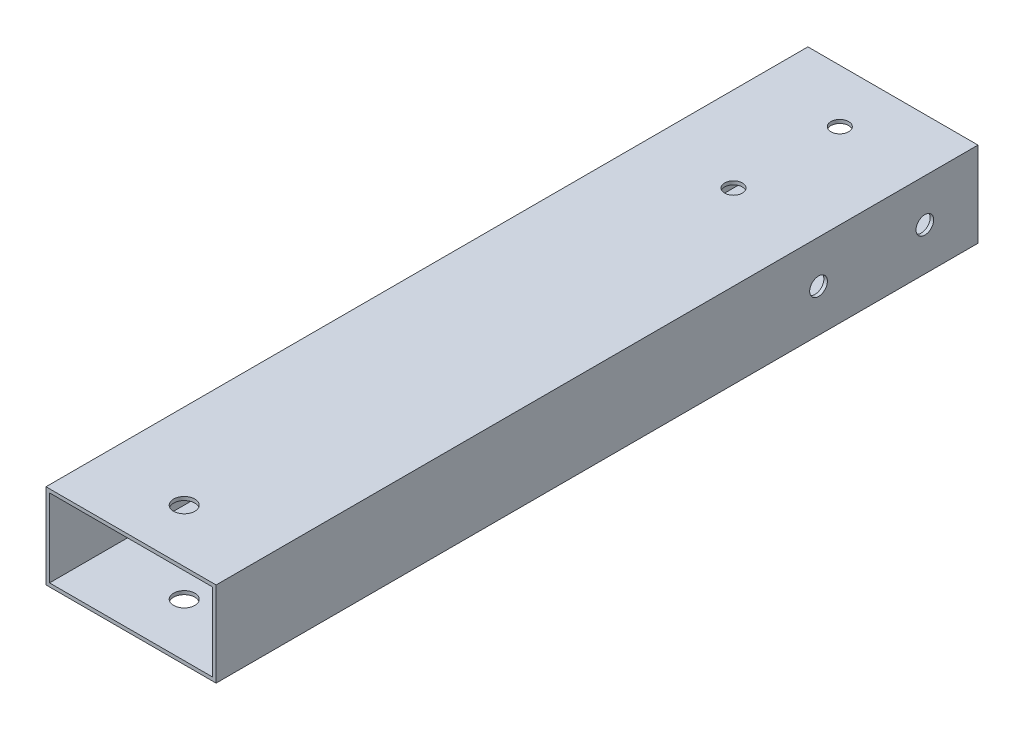
SolidWorks part; units mm, degrees
ref_plane "Front Plane" through (0, 0, 0) normal (0, 0, 1) x (1, 0, 0)
ref_plane "Top Plane" through (0, 0, 0) normal (0, 1, 0) x (1, 0, 0)
ref_plane "Right Plane" through (0, 0, 0) normal (1, 0, 0) x (0, 0, -1)
sketch "Sketch2" plane through (0, 0, 0) normal (0, 0, 1) x (1, 0, 0)
  line L0 (-23, 11) -> (-23, -11)
  line L1 (-24, 12) -> (24, 12)
  line L2 (-24, 12) -> (-24, -12)
  line L3 (-24, -12) -> (24, -12)
  line L4 (24, 12) -> (24, -12)
  line L5 (-24, 12) -> (24, -12) construction
  line L6 (-24, -12) -> (24, 12) construction
  line L7 (-23, -11) -> (23, -11)
  line L8 (23, 11) -> (23, -11)
  line L9 (-23, 11) -> (23, 11)
  point P0 (0, 0)
  dimension "D1" = 24
  dimension "D2" = 48
  dimension "D3" = 1
extrude "Boss-Extrude1" add sketch "Sketch2" along normal blind 240
sketch "Sketch4" plane through (0, -12, 0) normal (0, -1, 0) x (1, 0, 0)
  line L0 (-24, 240) -> (24, 240) construction
  line L1 (24, 240) -> (24, 0) construction
  circle A0 centre (0, 200) radius 3
  dimension "D2" = 6
  dimension "D3" = 24
  dimension "D1" = 40
extrude "Cut-Extrude1" cut sketch "Sketch4" against normal blind 240 contours A0
sketch "Sketch5" plane through (0, -12, 0) normal (0, -1, 0) x (1, 0, 0)
  line L0 (-9, 0) -> (9, 0)
  line L2 (-9, 0) -> (-9, 50)
  line L3 (-9, 50) -> (9, 50)
  line L4 (9, 0) -> (9, 50)
  line L5 (0, 50) -> (0, 0)
  circle A0 centre (0, 15) radius 2.5
  circle A1 centre (0, 45) radius 2.5
  point P0 (0, 0)
  point P8 (0, 0)
  dimension "D3" = 5
  dimension "D4" = 5
  dimension "D1" = 50
  dimension "D2" = 18
  dimension "D5" = 15
  dimension "D6" = 5
extrude "Cut-Extrude3" cut sketch "Sketch5" against normal blind 240 contours L5 A1 | L5 A1 | L5 A0 | L5 A0
sketch "Sketch7" plane through (24, 0, 0) normal (1, 0, 0) x (0, 0, -1)
  line L0 (0, -9) -> (0, 9)
  line L1 (0, -9) -> (-50, -9)
  line L2 (-50, -9) -> (-50, 9)
  line L3 (0, 9) -> (-50, 9)
  line L4 (-50, 0) -> (0, 0)
  circle A0 centre (-15, 0) radius 2.5
  circle A1 centre (-45, 0) radius 2.5
  point P0 (0, 0)
  point P7 (0, 0)
  dimension "D5" = 5
  dimension "D6" = 5
  dimension "D1" = 15
  dimension "D2" = 5
  dimension "D3" = 50
  dimension "D4" = 18
  dimension "D7" = 90
  dimension "D8" = 90
  dimension "D9" = 50
extrude "Cut-Extrude4" cut sketch "Sketch7" against normal blind 240 contours L4 A1 | L4 A1 | L4 A0 | L4 A0
sketch "Sketch8" plane through (0, -12, 0) normal (0, -1, 0) x (1, 0, 0)
  line L0 (24, 240) -> (24, 0) construction
  line L1 (-24, 240) -> (24, 240)
  line L2 (-24, 240) -> (-24, 215)
  line L3 (-24, 215) -> (24, 215)
  line L4 (24, 240) -> (24, 215)
  dimension "D1" = 25
extrude "Cut-Extrude5" cut sketch "Sketch8" against normal through all
equation "\"1ocm\"=1"
